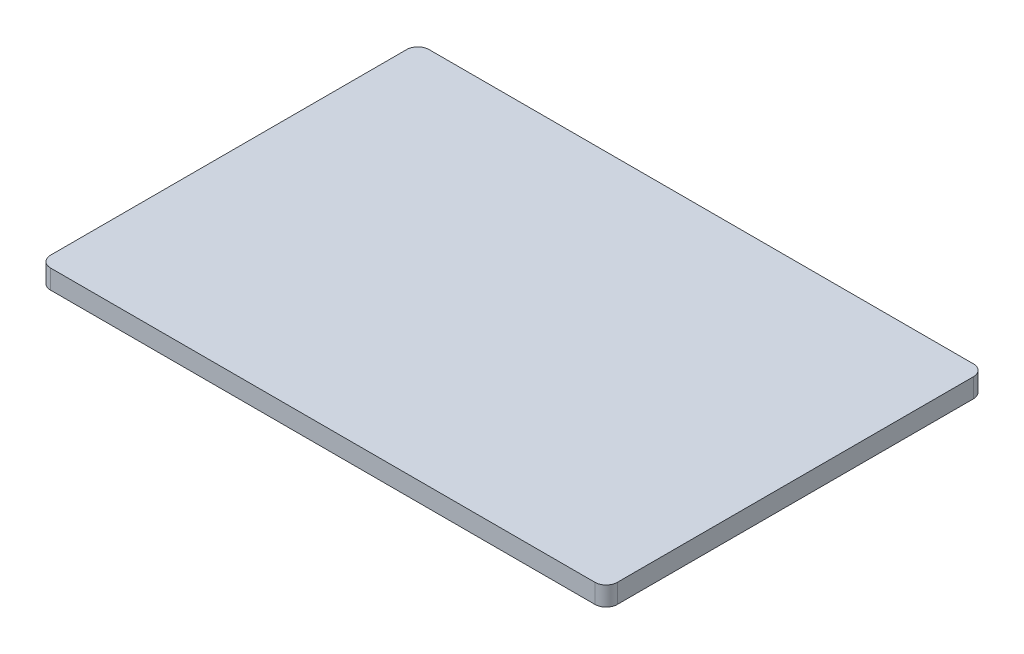
SolidWorks part; units mm, degrees
ref_plane "Front Plane" through (0, 0, 0) normal (0, 0, 1) x (1, 0, 0)
ref_plane "Top Plane" through (0, 0, 0) normal (0, 1, 0) x (1, 0, 0)
ref_plane "Right Plane" through (0, 0, 0) normal (1, 0, 0) x (0, 0, -1)
sketch "Sketch1" plane through (0, 0, 0) normal (0, 1, 0) x (1, 0, 0)
  line L1 (-44.5196, 29.813) -> (44.5196, 29.813)
  line L2 (-44.5196, 29.813) -> (-44.5196, -29.813)
  line L3 (-44.5196, -29.813) -> (44.5196, -29.813)
  line L4 (44.5196, 29.813) -> (44.5196, -29.813)
  line L5 (-44.5196, 29.813) -> (44.5196, -29.813) construction
  line L6 (-44.5196, -29.813) -> (44.5196, 29.813) construction
  point P0 (0, 0)
  dimension "D1" = 89.0392
  dimension "D2" = 59.626
extrude "Boss-Extrude1" add sketch "Sketch1" along normal blind 2.9972
fillet "Fillet1" radius 2 4 edges at (-44.5196, 1.4986, 29.813) (-44.5196, 1.4986, -29.813) (44.5196, 1.4986, -29.813) (44.5196, 1.4986, 29.813)
sketch "Sketch2" plane through (0, 2.9972, 0) normal (0, 1, 0) x (1, 0, 0)
  line L0 (-44.2656, 27.813) -> (-44.2656, -27.813)
  line L1 (-42.5196, -29.559) -> (42.5196, -29.559)
  line L2 (44.2656, -27.813) -> (44.2656, 27.813)
  line L3 (42.5196, 29.559) -> (-42.5196, 29.559)
  line L4 (-44.5196, 27.813) -> (-44.5196, -27.813)
  line L5 (-42.5196, -29.813) -> (42.5196, -29.813)
  line L6 (44.5196, -27.813) -> (44.5196, 27.813)
  line L7 (42.5196, 29.813) -> (-42.5196, 29.813)
  line L8 (-44.5196, 27.813) -> (-44.5196, -27.813) construction
  line L9 (-42.5196, -29.813) -> (42.5196, -29.813) construction
  line L10 (44.5196, -27.813) -> (44.5196, 27.813) construction
  line L11 (42.5196, 29.813) -> (-42.5196, 29.813) construction
  arc A0 (-44.2656, -27.813) -> (-42.5196, -29.559) centre (-42.5196, -27.813) ccw
  arc A1 (42.5196, -29.559) -> (44.2656, -27.813) centre (42.5196, -27.813) ccw
  arc A2 (44.2656, 27.813) -> (42.5196, 29.559) centre (42.5196, 27.813) ccw
  arc A3 (-42.5196, 29.559) -> (-44.2656, 27.813) centre (-42.5196, 27.813) ccw
  arc A4 (-44.5196, -27.813) -> (-42.5196, -29.813) centre (-42.5196, -27.813) ccw
  arc A5 (42.5196, -29.813) -> (44.5196, -27.813) centre (42.5196, -27.813) ccw
  arc A6 (44.5196, 27.813) -> (42.5196, 29.813) centre (42.5196, 27.813) ccw
  arc A7 (-42.5196, 29.813) -> (-44.5196, 27.813) centre (-42.5196, 27.813) ccw
  arc A8 (-44.5196, -27.813) -> (-42.5196, -29.813) centre (-42.5196, -27.813) ccw construction
  arc A9 (42.5196, -29.813) -> (44.5196, -27.813) centre (42.5196, -27.813) ccw construction
  arc A10 (44.5196, 27.813) -> (42.5196, 29.813) centre (42.5196, 27.813) ccw construction
  arc A11 (-42.5196, 29.813) -> (-44.5196, 27.813) centre (-42.5196, 27.813) ccw construction
  line M17 (-44.5196, 27.813) -> (-44.5196, -27.813)
  arc M18 (-44.5196, -27.813) -> (-42.5196, -29.813) centre (-42.5196, -27.813) ccw
  line M19 (-42.5196, -29.813) -> (42.5196, -29.813)
  arc M20 (42.5196, -29.813) -> (44.5196, -27.813) centre (42.5196, -27.813) ccw
  line M21 (44.5196, -27.813) -> (44.5196, 27.813)
  arc M22 (44.5196, 27.813) -> (42.5196, 29.813) centre (42.5196, 27.813) ccw
  line M23 (42.5196, 29.813) -> (-42.5196, 29.813)
  arc M24 (-42.5196, 29.813) -> (-44.5196, 27.813) centre (-42.5196, 27.813) ccw
  dimension "D1" = 0
  dimension "D2" = 0.254
extrude "Cut-Extrude1" cut sketch "Sketch2" against normal through all contours A3 L3 A2 L2 A1 L1 A0 L0 M24 M17 M18 M19 M20 M21 M22 M23
